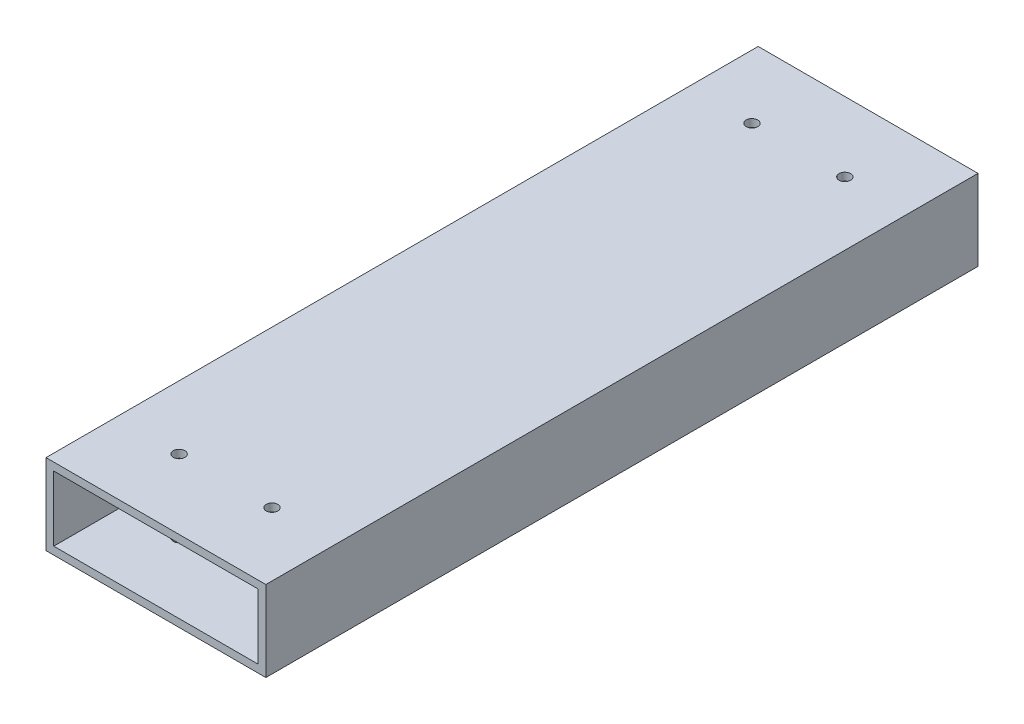
SolidWorks part; units mm, degrees
ref_plane "Alzado" through (0, 0, 0) normal (0, 0, 1) x (1, 0, 0)
ref_plane "Planta" through (0, 0, 0) normal (0, 1, 0) x (1, 0, 0)
ref_plane "Vista lateral" through (0, 0, 0) normal (1, 0, 0) x (0, 0, -1)
sketch "Croquis1" plane through (0, 0, 0) normal (0, 0, 1) x (1, 0, 0)
  line L1 (37.1385, -197.0638) -> (-19.6615, -197.0638)
  line L2 (37.1385, -197.0638) -> (37.1385, -217.8838)
  line L3 (37.1385, -217.8838) -> (-19.6615, -217.8838)
  line L4 (-19.6615, -197.0638) -> (-19.6615, -217.8838)
extrude "Saliente-Extruir1" add sketch "Croquis1" along normal blind 184
sketch "Croquis5" plane through (0, 0, 0) normal (0, 0, -1) x (-1, 0, 0)
  line L7 (-35.1385, -199.0638) -> (17.6615, -199.0638)
  line L8 (-35.1385, -199.0638) -> (-35.1385, -215.8838)
  line L9 (-35.1385, -215.8838) -> (17.6615, -215.8838)
  line L10 (17.6615, -199.0638) -> (17.6615, -215.8838)
  point P6 (-8.7385, -207.4738)
extrude "Cortar-Extruir5" cut sketch "Croquis5" against normal up to surface (184 mm away) up to face at (8.7385, -207.4738, 184)
sketch "Croquis6" plane through (0, -197.0638, 0) normal (0, 1, 0) x (1, 0, 0)
  circle A0 centre (-3.2615, -18) radius 1.5
  circle A1 centre (20.7385, -18) radius 1.5
  circle A2 centre (-3.2615, -166) radius 1.5
  circle A3 centre (20.7385, -166) radius 1.5
extrude "Cortar-Extruir6" cut sketch "Croquis6" against normal blind 26
